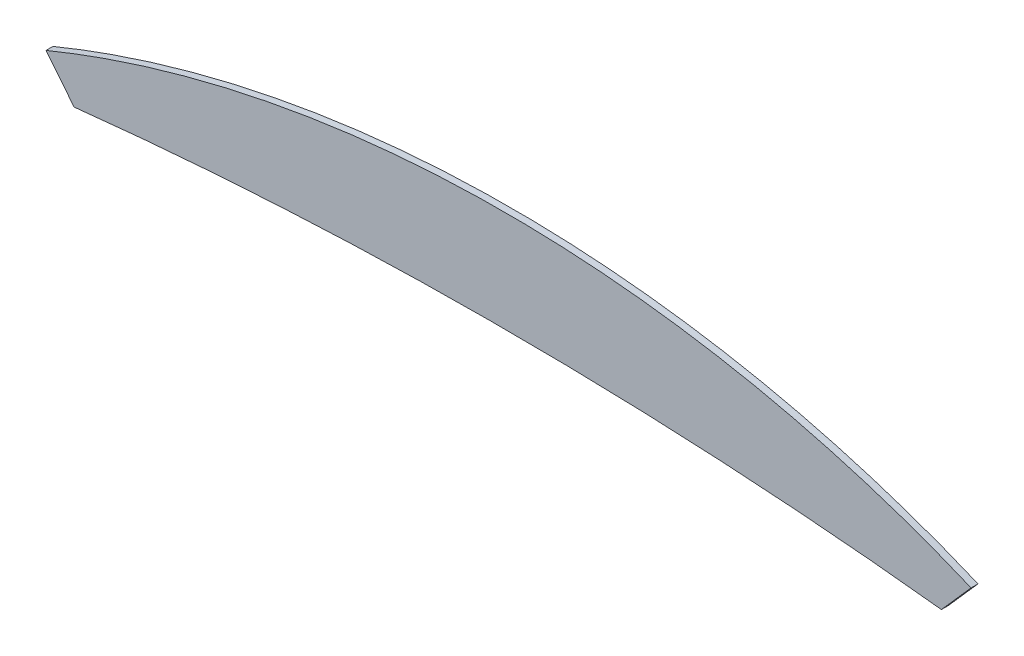
SolidWorks part; units mm, degrees
ref_plane "Alzado" through (0, 0, 0) normal (0, 0, 1) x (1, 0, 0)
ref_plane "Planta" through (0, 0, 0) normal (0, 1, 0) x (1, 0, 0)
ref_plane "Vista lateral" through (0, 0, 0) normal (1, 0, 0) x (0, 0, -1)
sketch "Model" plane through (0, 0, 0) normal (0, 0, 1) x (1, 0, 0)
  spline S0 degree 2 poles (45.6835, 30.1136) (45.4804, 30.3665) (45.2773, 30.6193) knots 2.235743 2.235743 2.235743 3.235743 3.235743 3.235743 weights 1 1 1
  spline S1 degree 2 poles (58.2118, 30.0913) (51.9496, 30.7936) (45.6835, 30.1136) knots 1.961654 1.961654 1.961654 2.235743 2.235743 2.235743 weights 1 0.990624 1
  spline S2 degree 2 poles (58.6404, 30.5771) (58.4261, 30.3342) (58.2118, 30.0913) knots 0.961654 0.961654 0.961654 1.961654 1.961654 1.961654 weights 1 1 1
  spline S3 degree 2 poles (45.2773, 30.6193) (51.9726, 33.3866) (58.6404, 30.5771) knots 0 0 0 0.961654 0.961654 0.961654 weights 1 0.886613 1
extrude "Saliente-Extruir1" add sketch "Model" along normal blind 0.1
